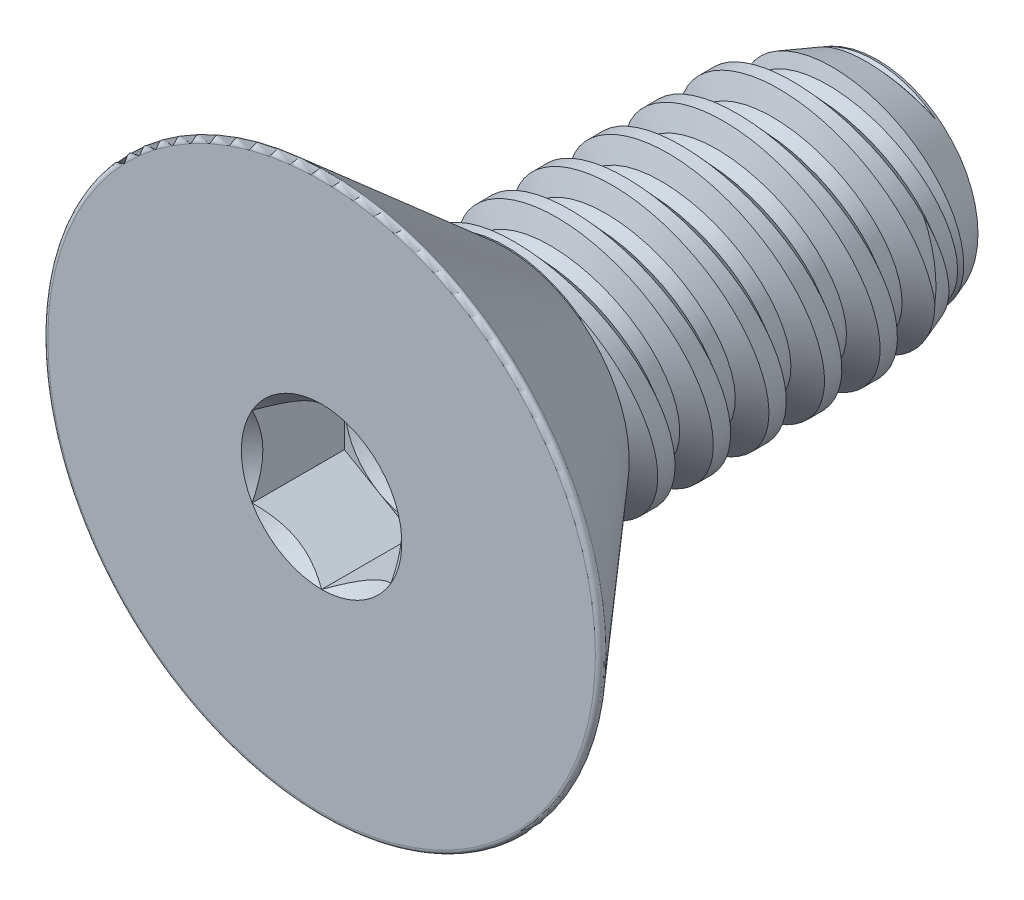
SolidWorks part; units mm, degrees
ref_plane "Front" through (0, 0, 0) normal (0, 0, 1) x (1, 0, 0)
ref_plane "Top" through (0, 0, 0) normal (0, 1, 0) x (1, 0, 0)
ref_plane "Right" through (0, 0, 0) normal (1, 0, 0) x (0, 0, -1)
sketch "Sketch1" plane through (0, 0, 0) normal (1, 0, 0) x (0, 0, -1)
  line L0 (0, 0) -> (-2.1082, 0) construction
  line L1 (0, 0) -> (4.2418, 0)
  line L2 (0, 0) -> (0, 1.4224)
  line L3 (0, 1.4224) -> (4.2418, 1.4224)
  line L4 (4.2418, 0) -> (4.2418, 1.4224)
  line L5 (0, -1.4224) -> (4.2418, -1.4224) construction
  dimension "D1" = 4.2418
  dimension "Thread Dia" = 2.8448
  dimension "Length" = 6.35
  dimension "Head Height" = 2.1082
revolve "Revolve1" add sketch "Sketch1" angle 360 about L0
ref_plane "Plane1" through (0, 0, 2.1082) normal (0, 0, 1) x (1, 0, 0)
sketch "Sketch2" plane through (0, 0, 0) normal (1, 0, 0) x (0, 0, -1)
  line L0 (0, 1.4224) -> (0, -1.4224) construction
  line L1 (0, -1.4224) -> (0.635, -1.4224) construction
  line L2 (0.635, -1.4224) -> (0, 1.4224) construction
  line L3 (0, 1.4224) -> (0.0775, 1.4397) construction
  line L4 (0.0775, 1.4397) -> (0.6197, 1.5607)
  line L5 (0.6197, 1.5607) -> (0.501, 1.1821)
  line L6 (0.501, 1.1821) -> (0.346, 1.1475)
  line L7 (0.346, 1.1475) -> (0.0775, 1.4397)
  line L8 (0.4235, 1.1648) -> (0.3486, 1.5002) construction
  line L9 (0, -1.4224) -> (4.2418, -1.4224) construction
  line L10 (0, 1.4224) -> (4.2418, 1.4224) construction
  line L12 (0.366, 1.4224) -> (1.001, -1.4224) construction
  line L13 (0, -0.1526) -> (1.367, 0.1526) construction
  line L15 (0, 0) -> (0, 1.4224) construction
  point P19 (0.6835, 0)
  dimension "D1" = 60
  dimension "Thread Pitch" = 0.635
  dimension "D2" = 0.0794
  dimension "D3" = 0.1588
  dimension "D4" = 0.635
revolve "Cut-Revolve1" cut sketch "Sketch2" angle 360 about L13
sketch "Sketch3" plane through (0, 0, 0) normal (1, 0, 0) x (0, 0, -1)
  line L0 (4.2418, 1.1475) -> (3.4864, 1.4224)
  line L1 (3.4864, 1.4224) -> (4.2418, 1.4224)
  line L2 (4.2418, 1.4224) -> (4.2418, 1.1475)
  line L3 (0, 1.4224) -> (4.2418, 1.4224) construction
  line L4 (4.2418, 0) -> (4.2418, 1.4224) construction
  line L5 (3.4864, 0) -> (0, 0) construction
  line L6 (3.4864, 1.4224) -> (3.4864, -1.4224) construction
  line L7 (0, -1.4224) -> (4.2418, -1.4224) construction
  dimension "D1" = 20
  dimension "D2" = 2.8448
revolve "Cut-Revolve2" cut sketch "Sketch3" angle 360 about L5
pattern_linear "LPattern1" count 7 spacing 0.635 along (0, 0, 1)
pattern_linear "LPattern2" count 2 spacing 0.635 along (0, 0, 1)
sketch "Sketch4" plane through (0, 0, 0) normal (0, 0, 1) x (1, 0, 0)
  circle A0 centre (0, 0) radius 3.2385
  dimension "Head Dia" = 6.477
extrude "Extrude1" add sketch "Sketch4" along normal up to surface (2.1082 mm away)
sketch "Sketch9" plane through (0, 0, 0) normal (1, 0, 0) x (0, 0, -1)
  line L0 (-2.1082, 3.2385) -> (0, 1.4059)
  line L1 (0, 1.4059) -> (0, 3.2385)
  line L2 (0, 3.2385) -> (-2.1082, 3.2385)
  line L3 (0, 0) -> (-2.1082, 0) construction
  line L6 (-2.1082, -3.2385) -> (0, -1.4059) construction
  line L7 (0, -3.2385) -> (0, 3.2385) construction
  line L8 (-2.1082, 3.2385) -> (-2.1082, -3.2385) construction
  line L9 (0, 3.2385) -> (-2.1082, 3.2385) construction
  dimension "D1" = 82
revolve "Cut-Revolve3" cut sketch "Sketch9" angle 360 about L3
fillet "Fillet1" radius 0.0508
sketch "Sketch6" plane through (0, 0, 2.1082) normal (0, 0, 1) x (1, 0, 0)
  line L1 (0, -0.9165) -> (0.7937, -0.4583)
  line L2 (0.7937, -0.4583) -> (0.7937, 0.4583)
  line L3 (0.7937, 0.4583) -> (0, 0.9165)
  line L4 (0, 0.9165) -> (-0.7938, 0.4583)
  line L5 (-0.7938, 0.4583) -> (-0.7938, -0.4583)
  line L6 (-0.7938, -0.4583) -> (0, -0.9165)
  circle A0 centre (0, 0) radius 0.7938 construction
  dimension "Hex" = 1.5875
extrude "Cut-Extrude1" cut sketch "Sketch6" against normal blind 1.0541
sketch "Sketch7" plane through (0, 0, 2.1082) normal (0, 0, 1) x (1, 0, 0)
  circle A0 centre (0, 0) radius 0.9165
extrude "Cut-Extrude4" cut sketch "Sketch7" against normal blind 1.0541 draft 45
sketch "Sketch8" plane through (0, 0, 1.0541) normal (0, 0, 1) x (1, 0, 0)
  circle A0 centre (0, 0) radius 0.7938 construction
  circle A1 centre (0, 0) radius 0.7938
extrude "Cut-Extrude5" cut sketch "Sketch8" against normal blind 0.3514 draft 60
equation "\"D2@Sketch2\"=\"Thread Pitch@Sketch2\"/8"
equation "\"D3@Sketch2\"=\"Thread Pitch@Sketch2\"/4"
equation "\"D4@Sketch2\"=\"Thread Pitch@Sketch2\""
equation "\"D3@LPattern1\"=\"Thread Pitch@Sketch2\""
equation "\"D1@Cut-Extrude1\"=\"Head Height@Sketch1\"/2"
equation "\"D1@Cut-Extrude4\"=\"D1@Cut-Extrude1\""
equation "\"D1@Cut-Extrude5\"=\"D1@Cut-Extrude1\"/3"
equation "\"D1@LPattern1\"=\"D1@Sketch1\"/\"Thread Pitch@Sketch2\""
equation "\"D3@LPattern2\"=\"Thread Pitch@Sketch2\""
